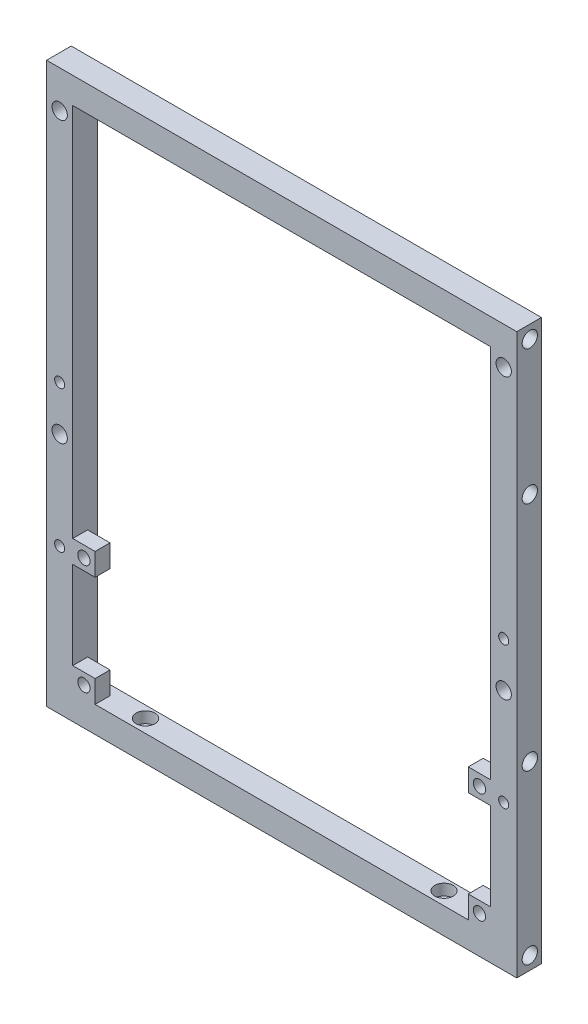
SolidWorks part; units mm, degrees
ref_plane "Front Plane" through (0, 0, 0) normal (0, 0, 1) x (1, 0, 0)
ref_plane "Top Plane" through (0, 0, 0) normal (0, 1, 0) x (1, 0, 0)
ref_plane "Right Plane" through (0, 0, 0) normal (1, 0, 0) x (0, 0, -1)
sketch "Sketch1" plane through (0, 0, 0) normal (0, 0, 1) x (1, 0, 0)
  line L1 (-63, -75) -> (63, -75)
  line L2 (-63, -75) -> (-63, 75)
  line L3 (-63, 75) -> (63, 75)
  line L4 (63, -75) -> (63, 75)
  line L5 (-63, -75) -> (63, 75) construction
  line L6 (-63, 75) -> (63, -75) construction
  line L7 (-56, -68) -> (56, -68)
  line L8 (-56, -68) -> (-56, 68)
  line L9 (-56, 68) -> (56, 68)
  line L10 (56, -68) -> (56, 68)
  line L11 (-56, -68) -> (56, 68) construction
  line L12 (-56, 68) -> (56, -68) construction
  point P0 (0, 0)
  point P6 (0, 0)
  dimension "D1" = 126
  dimension "D2" = 150
  dimension "D3" = 7
  dimension "D4" = 7
extrude "Boss-Extrude1" add sketch "Sketch1" along normal blind 7
sketch "Sketch2" plane through (-63, 0, 0) normal (-1, 0, 0) x (0, 0, 1)
  line L0 (3.5, 71.5) -> (3.5, -71.5) construction
  line L1 (7, 75) -> (0, 75) construction
  circle A0 centre (3.5, -71.5) radius 2.05
  circle A2 centre (3.5, 71.5) radius 2.05
  circle A3 centre (3.5, 35.5) radius 2.05
  circle A4 centre (3.5, -26.5) radius 2.05
  point P2 (3.5, 0)
  point P7 (3.5, 75)
  dimension "D2" = 4.1
  dimension "D3" = 36
  dimension "D4" = 45
  dimension "D1" = 3.5
extrude "Cut-Extrude1" cut sketch "Sketch2" against normal blind 6
mirror "Mirror1" about plane through (0, 0, 0) normal (1, 0, 0) of "Cut-Extrude1"
sketch "Sketch3" plane through (0, -68, 0) normal (0, 1, 0) x (1, 0, 0)
  line L0 (0, 0) -> (0, -7) construction
  line L1 (-56, 0) -> (56, 0) construction
  line L2 (-56, -7) -> (56, -7) construction
  line L3 (40, -3.5) -> (-40, -3.5) construction
  circle A0 centre (40, -3.5) radius 1.35
  circle A1 centre (-40, -3.5) radius 1.35
  point P9 (0, -3.5)
  dimension "D1" = 2.7
  dimension "D2" = 80
extrude "Cut-Extrude2" cut sketch "Sketch3" against normal through all
sketch "Sketch4" plane through (0, -68, 0) normal (0, 1, 0) x (1, 0, 0)
  circle A0 centre (40, -3.5) radius 2.5
  circle A1 centre (-40, -3.5) radius 2.5
  dimension "D1" = 5
extrude "Cut-Extrude3" cut sketch "Sketch4" against normal blind 3
sketch "Sketch5" plane through (0, 0, 0) normal (0, 0, -1) x (-1, 0, 0)
  line L0 (-59.5, -75) -> (-59.5, 75) construction
  line L1 (63, -75) -> (-63, -75) construction
  line L2 (-63, 75) -> (63, 75) construction
  line L3 (-56, 0) -> (-63, 0) construction
  line L4 (-56, -68) -> (-56, 68) construction
  line L5 (-63, -75) -> (-63, 75) construction
  line L6 (0, 75) -> (0, -75) construction
  line L7 (56, -68) -> (-56, -68) construction
  circle A0 centre (-59.5, 2) radius 1.35
  circle A1 centre (59.5, 2) radius 1.35
  circle A2 centre (-59.5, -36) radius 1.35
  circle A3 centre (59.5, -36) radius 1.35
  point P12 (-59.5, 0)
  point P13 (-59.5, 0)
  dimension "D1" = 2.7
  dimension "D2" = 2
  dimension "D3" = 32
extrude "Cut-Extrude4" cut sketch "Sketch5" against normal through all
sketch "Sketch6" plane through (0, 0, 0) normal (0, 0, -1) x (-1, 0, 0)
  circle A0 centre (-59.5, 2) radius 2.5
  circle A1 centre (59.5, 2) radius 2.5
  circle A2 centre (-59.5, -36) radius 2.5
  circle A3 centre (59.5, -36) radius 2.5
  dimension "D1" = 5
extrude "Cut-Extrude5" cut sketch "Sketch6" against normal blind 3
sketch "Sketch7" plane through (0, 0, 0) normal (0, 0, -1) x (-1, 0, 0)
  line L0 (-56, 68) -> (-63, 68) construction
  line L1 (-63, -75) -> (-63, 75) construction
  line L2 (-59.5, 65) -> (-59.5, -10) construction
  line L3 (-63, 75) -> (63, 75) construction
  circle A0 centre (-59.5, 65) radius 2.05
  circle A1 centre (-59.5, -10) radius 2.05
  point P8 (-59.5, 68)
  dimension "D1" = 4.1
  dimension "D2" = 10
  dimension "D3" = 75
extrude "Cut-Extrude6" cut sketch "Sketch7" against normal through all
mirror "Mirror2" about plane through (0, 0, 0) normal (1, 0, 0) of "Cut-Extrude6"
sketch "Sketch8" plane through (0, 0, 3) normal (0, 0, -1) x (-1, 0, 0)
  line L2 (-60.85, -0.1042) -> (-60.85, 4.1042)
  line L4 (-58.15, -0.1042) -> (-58.15, 4.1042)
  line L5 (-60.85, -0.1042) -> (-58.15, 4.1042) construction
  line L6 (-60.85, 4.1042) -> (-58.15, -0.1042) construction
  line L8 (-60.85, -38.1042) -> (-60.85, -33.8958)
  line L10 (-58.15, -38.1042) -> (-58.15, -33.8958)
  line L11 (-60.85, -38.1042) -> (-58.15, -33.8958) construction
  line L12 (-60.85, -33.8958) -> (-58.15, -38.1042) construction
  circle A0 centre (-59.5, 2) radius 2.5 construction
  circle A1 centre (-59.5, -36) radius 2.5 construction
  circle A2 centre (-59.5, -36) radius 2.5 construction
  arc A3 (-58.15, 4.1042) -> (-60.85, 4.1042) centre (-59.5, 2) ccw
  arc A4 (-58.15, -33.8958) -> (-60.85, -33.8958) centre (-59.5, -36) ccw
  circle A5 centre (-59.5, 2) radius 1.35 construction
  circle A6 centre (-59.5, -36) radius 1.35 construction
  arc A7 (-60.85, -38.1042) -> (-58.15, -38.1042) centre (-59.5, -36) ccw
  arc A8 (-60.85, -0.1042) -> (-58.15, -0.1042) centre (-59.5, 2) ccw
  point P0 (-59.5, 2)
  point P8 (-59.5, -36)
extrude "Cut-Extrude7" cut sketch "Sketch8" against normal blind 0.2
sketch "Sketch9" plane through (0, 0, 3.2) normal (0, 0, -1) x (-1, 0, 0)
  line L0 (-58.15, 2) -> (-58.15, 4.1042) construction
  line L1 (-60.85, 0.65) -> (-58.15, 0.65)
  line L2 (-60.85, 0.65) -> (-60.85, 3.35)
  line L3 (-60.85, 3.35) -> (-58.15, 3.35)
  line L4 (-58.15, 0.65) -> (-58.15, 3.35)
  line L5 (-60.85, 0.65) -> (-58.15, 3.35) construction
  line L6 (-60.85, 3.35) -> (-58.15, 0.65) construction
  line L7 (-58.15, -38.1042) -> (-58.15, -33.8958) construction
  line L8 (-60.85, -37.35) -> (-58.15, -37.35)
  line L9 (-60.85, -37.35) -> (-60.85, -34.65)
  line L10 (-60.85, -34.65) -> (-58.15, -34.65)
  line L11 (-58.15, -37.35) -> (-58.15, -34.65)
  line L12 (-60.85, -37.35) -> (-58.15, -34.65) construction
  line L13 (-60.85, -34.65) -> (-58.15, -37.35) construction
  arc A0 (-58.15, 2) -> (-60.85, 2) centre (-59.5, 2) ccw construction
  point P0 (-59.5, 2)
  point P8 (-59.5, -36)
extrude "Cut-Extrude8" cut sketch "Sketch9" against normal blind 0.2
mirror "Mirror3" about plane through (0, 0, 0) normal (1, 0, 0) of "Cut-Extrude8", "Cut-Extrude7"
sketch "Sketch10" plane through (0, 0, 7) normal (0, 0, 1) x (1, 0, 0)
  line L0 (56, -68) -> (56, 68) construction
  line L1 (56, -68) -> (50, -68)
  line L2 (56, -68) -> (56, -62)
  line L3 (56, -62) -> (50, -62)
  line L4 (50, -68) -> (50, -62)
  line L5 (56, -38.5) -> (50, -38.5)
  line L6 (56, -38.5) -> (56, -32.5)
  line L7 (56, -32.5) -> (50, -32.5)
  line L8 (50, -38.5) -> (50, -32.5)
  line L9 (-56, -68) -> (56, -68) construction
  dimension "D1" = 6
  dimension "D2" = 35.5
extrude "Boss-Extrude2" add sketch "Sketch10" against normal offset from surface (4 mm away) 3 up to face at (-57.45, -10, 0)
sketch "Sketch11" plane through (0, 0, 3) normal (0, 0, -1) x (-1, 0, 0)
  line L0 (-56, -38.5) -> (-50, -32.5) construction
  line L2 (-56, -68) -> (-50, -62) construction
  circle A0 centre (-53, -35.5) radius 1.65
  circle A1 centre (-53, -65) radius 1.65
  dimension "D1" = 3.3
extrude "Cut-Extrude9" cut sketch "Sketch11" against normal through all
mirror "Mirror4" about plane through (0, 0, 0) normal (1, 0, 0) of "Cut-Extrude9", "Boss-Extrude2"
chamfer "Chamfer1" distance 0.4 angle 45 4 edges at (-56, 0, 0) (0, 68, 0) (56, 0, 0) (0, -68, 0)
chamfer "Chamfer2" distance 0.4 angle 45 4 edges at (0, 75, 0) (-63, 0, 0) (0, -75, 0) (63, 0, 0)
